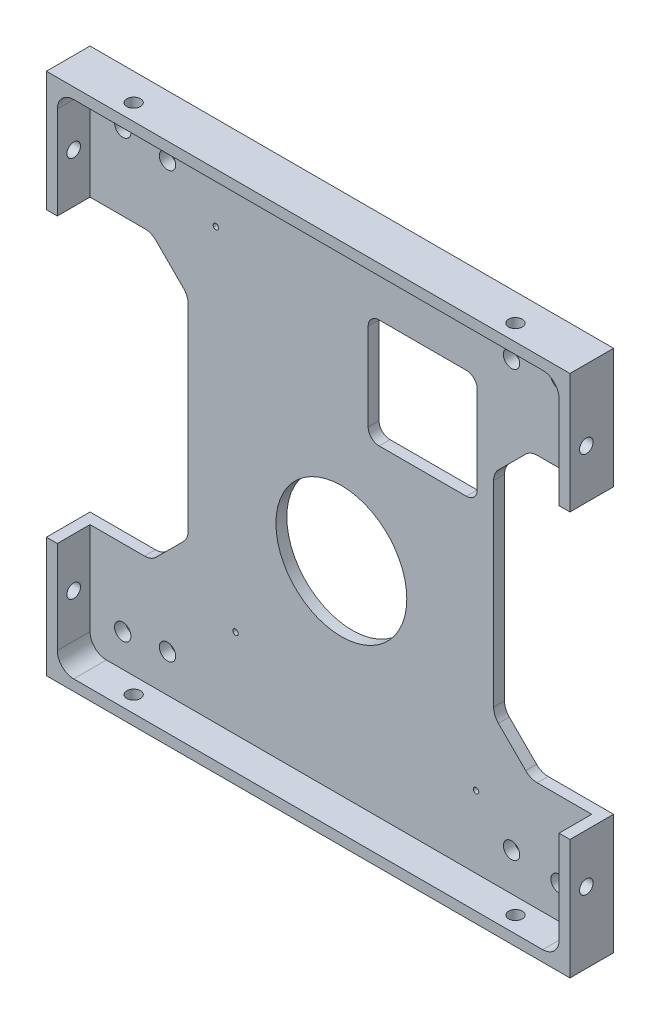
SolidWorks part; units mm, degrees
material "6061-T6 (SS)"
ref_plane "Front" through (0, 0, 0) normal (0, 0, 1) x (1, 0, 0)
ref_plane "Top" through (0, 0, 0) normal (0, 1, 0) x (1, 0, 0)
ref_plane "Right" through (0, 0, 0) normal (1, 0, 0) x (0, 0, -1)
sketch "Sketch1" plane through (0, 0, 0) normal (0, 0, 1) x (1, 0, 0)
  line L1 (-48, -48) -> (48, -48)
  line L2 (-48, -48) -> (-48, 48)
  line L3 (-48, 48) -> (48, 48)
  line L4 (48, -48) -> (48, 48)
  line L5 (-48, -48) -> (48, 48) construction
  line L6 (-48, 48) -> (48, -48) construction
  point P0 (0, 0)
  dimension "D1" = 96
  dimension "D2" = 96
extrude "Boss-Extrude1" add sketch "Sketch1" along normal blind 8
sketch "Sketch2" plane through (0, 0, 8) normal (0, 0, 1) x (1, 0, 0)
  line L1 (46, -46) -> (-46, -46)
  line L2 (46, -46) -> (46, 46)
  line L3 (46, 46) -> (-46, 46)
  line L4 (-46, -46) -> (-46, 46)
  line L5 (46, -46) -> (-46, 46) construction
  line L6 (46, 46) -> (-46, -46) construction
  point P0 (0, 0)
  dimension "D1" = 92
  dimension "D2" = 92
extrude "Component Platform" cut sketch "Sketch2" against normal blind 6
sketch "Sketch3" plane through (0, 0, 2) normal (0, 0, 1) x (1, 0, 0)
  line L1 (-33.8787, -25.1213) -> (-28.8787, -20.1213)
  line L2 (-33.8787, 25.1213) -> (-28.8787, 20.1213)
  line L3 (-28, -18) -> (-28, 18)
  line L4 (-48, -26) -> (-36, -26)
  line L7 (-48, 48) -> (-48, -48) construction
  line L8 (0, -56.7987) -> (0, 73.4321) construction
  line L9 (46, -46) -> (-57.8147, 57.8147) construction
  line L18 (46, 46) -> (-68.5705, -68.5705) construction
  line L23 (-48, 26) -> (-36, 26)
  line L26 (-48, -26) -> (-48, 26)
  line L28 (-48, -48) -> (48, -48) construction
  line L29 (48, -26) -> (48, 26)
  line L30 (48, 26) -> (36, 26)
  line L31 (33.8787, 25.1213) -> (28.8787, 20.1213)
  line L32 (28, -18) -> (28, 18)
  line L33 (33.8787, -25.1213) -> (28.8787, -20.1213)
  line L34 (48, -26) -> (36, -26)
  arc A3 (-28.8787, -20.1213) -> (-28, -18) centre (-31, -18) ccw
  arc A4 (-28.8787, 20.1213) -> (-28, 18) centre (-31, 18) cw
  arc A13 (-33.8787, -25.1213) -> (-36, -26) centre (-36, -23) cw
  arc A15 (-33.8787, 25.1213) -> (-36, 26) centre (-36, 23) ccw
  arc A17 (33.8787, 25.1213) -> (36, 26) centre (36, 23) cw
  arc A18 (28.8787, 20.1213) -> (28, 18) centre (31, 18) ccw
  arc A19 (28.8787, -20.1213) -> (28, -18) centre (31, -18) cw
  arc A20 (33.8787, -25.1213) -> (36, -26) centre (36, -23) ccw
  point P0 (-48, 0)
  point P37 (-48, 0)
  dimension "D2" = 3
  dimension "D3" = 3
  dimension "D4" = 20
  dimension "D6" = 3
  dimension "D7" = 3
  dimension "D8" = 135
  dimension "D5" = 52
  dimension "D9" = 135
  dimension "D10" = 12
  dimension "D11" = 12
  dimension "D12" = 48
extrude "Cable Slots" cut sketch "Sketch3" against normal mid plane 12
ref_plane "Center Y-Plane" through (0, 0, 0) normal (1, 0, 0) x (0, 0, -1)
ref_plane "Center X-Plane" through (0, 0, 0) normal (0, -1, 0) x (-1, 0, 0)
fillet "Inner Corner Fillets" radius 3 4 edges at (46, -46, 5) (-46, -46, 5) (46, 46, 5) (-46, 46, 5)
sketch "Sketch7" plane through (0, 0, 2) normal (0, 0, 1) x (1, 0, 0)
  line L0 (-48, -48) -> (48, -48) construction
  line L4 (48, -48) -> (48, -26) construction
  line L5 (48, 26) -> (48, 48) construction
  line L7 (48, 48) -> (-48, 48) construction
  line L8 (-43, -46) -> (43, -46) construction
  point P1 (-19.32, -29.75)
  point P4 (24.78, -32.85)
  point P5 (24.78, 32.85)
  point P8 (-22.92, 32.85)
  point P12 (24.7, -56.85)
  point P13 (24.7, 48)
  point P14 (-19.4, -48)
  point P15 (48, -32.85)
  point P16 (-48, -32.85)
  point P18 (-19.4, 48)
  point P19 (48, -32.85)
  point P20 (-48, -32.85)
  point P24 (48, 43.7)
  point P25 (-48.7506, 43.7)
  point P27 (48, 32.85)
  point P28 (-23, -48)
  point P29 (-23, 48)
  point P31 (-48.7506, 32.85)
  dimension "D1" = 16.25
  dimension "D2" = 47.7
  dimension "D3" = 15.15
  dimension "D4" = 23.22
  dimension "D5" = 23.22
  dimension "D6" = 44.1
  dimension "D7" = 15.15
  dimension "D8" = 15.15
sketch "Sketch9" plane through (0, 0, 2) normal (0, 0, 1) x (1, 0, 0)
  line L0 (25, 31) -> (25, 15)
  line L1 (23, 33) -> (7, 33)
  line L2 (23, 13) -> (7, 13)
  line L5 (5, 15) -> (5, 31)
  line L6 (48, 26) -> (48, 48) construction
  line L8 (48, 48) -> (-48, 48) construction
  arc A1 (25, 15) -> (23, 13) centre (23, 15) cw
  arc A2 (25, 31) -> (23, 33) centre (23, 31) ccw
  arc A3 (7, 33) -> (5, 31) centre (7, 31) ccw
  arc A4 (5, 15) -> (7, 13) centre (7, 15) ccw
  point P15 (25, 33)
  dimension "D1" = 2
  dimension "D6" = 2
  dimension "D7" = 16
  dimension "D2" = 20
  dimension "D3" = 16
  dimension "D4" = 15
  dimension "D5" = 23
sketch "Sketch11" plane through (48, 0, 0) normal (1, 0, 0) x (0, 0, -1)
  line L0 (-5, -48) -> (-5, 48) construction
  line L1 (-8, -48) -> (0, -48) construction
  line L2 (-8, 48) -> (0, 48) construction
  line L3 (-8, -48) -> (-8, -26) construction
  dimension "D1" = 3
sketch "Sketch12" plane through (0, 48, 0) normal (0, 1, 0) x (1, 0, 0)
  line L0 (-48, -5) -> (48, -5) construction
  line L1 (-48, -8) -> (-48, 0) construction
  line L2 (48, -8) -> (48, 0) construction
  line L3 (48, -8) -> (-48, -8) construction
  dimension "D1" = 3
hole_wizard "M3x0.5 Tapped Hole1" positions "Sketch13" profile "Sketch14" tap size "M3x0.5" standard "ANSI Metric"
sketch "Sketch13" plane through (48, 0, 0) normal (1, 0, 0) x (0, 0, -1)
  line L0 (-5, -48) -> (-5, 48) construction
  point P0 (-5, -35)
  point P4 (-5, 35)
  dimension "D1" = 70
  dimension "D2" = 35
sketch "Sketch14" plane through (48, -35, 5) normal (0, 1, 0) x (0, 0, -1)
  line L0 (0, 0) -> (0, 10.7511)
  line L1 (0, 10.7511) -> (1.25, 10)
  line L2 (1.25, 10) -> (1.25, 0)
  line L5 (1.25, 0) -> (0, 0)
  line L10 (0, 10.7511) -> (-1.25, 10) construction
  line L11 (0, -6.35) -> (0, 107.95) construction
  dimension "Tap Drill Dia." = 2.5
  dimension "Tap Drill Depth" = 10
  dimension "Drill Angle" = 118
hole_wizard "M3x0.5 Tapped Hole2" positions "Sketch15" profile "Sketch16" tap size "M3x0.5" standard "ANSI Metric"
sketch "Sketch15" plane through (0, 48, 0) normal (0, 1, 0) x (1, 0, 0)
  line L0 (-48, -5) -> (48, -5) construction
  point P0 (35, -5)
  point P4 (-35, -5)
  dimension "D1" = 70
  dimension "D2" = 35
sketch "Sketch16" plane through (35, 48, 5) normal (1, 0, 0) x (0, 0, 1)
  line L0 (0, 0) -> (0, 10.7511)
  line L1 (0, 10.7511) -> (1.25, 10)
  line L2 (1.25, 10) -> (1.25, 0)
  line L5 (1.25, 0) -> (0, 0)
  line L10 (0, 10.7511) -> (-1.25, 10) construction
  line L11 (0, -6.35) -> (0, 107.95) construction
  dimension "Tap Drill Dia." = 2.5
  dimension "Tap Drill Depth" = 10
  dimension "Drill Angle" = 118
mirror "Mirror1" about plane through (0, 0, 0) normal (1, 0, 0) of "M3x0.5 Tapped Hole1"
mirror "Mirror2" about plane through (0, 0, 0) normal (0, -1, 0) of "M3x0.5 Tapped Hole2"
sketch "Sketch22" plane through (0, 0, 2) normal (0, 0, 1) x (1, 0, 0)
  line L2 (46, -43) -> (46, -26) construction
  line L3 (-43, -46) -> (43, -46) construction
  line L4 (-46, -26) -> (-46, -43) construction
  line L6 (46, 26) -> (46, 43) construction
  line L7 (43, 46) -> (-43, 46) construction
  line L8 (-46, 43) -> (-46, 26) construction
  point P0 (-31.791, -39.06)
  point P1 (-31.791, 38.94)
  point P2 (31.29, 38.94)
  point P3 (31.29, -39.06)
  dimension "D1" = 14.71
  dimension "D2" = 6.94
  dimension "D3" = 6.94
  dimension "D4" = 14.209
  dimension "D5" = 14.71
  dimension "D6" = 7.06
  dimension "D7" = 7.06
  dimension "D8" = 14.209
hole_wizard "Ø1.0mm Dowel Hole1" positions "Sketch27" profile "Sketch28" hole size "Ø1.0" standard "ANSI Metric"
sketch "Sketch27" plane through (0, 0, 2) normal (0, 0, 1) x (1, 0, 0)
  point P0 (-19.32, -29.75)
  point P3 (24.78, -32.85)
  point P9 (-22.92, 32.85)
sketch "Sketch28" plane through (-19.32, -29.75, 2) normal (1, 0, 0) x (0, -1, 0)
  line L0 (0, 0) -> (0, 4.0004)
  line L1 (0, 4.0004) -> (0.5, 3.7)
  line L2 (0.5, 3.7) -> (0.5, 0)
  line L5 (0.5, 0) -> (0, 0)
  line L10 (0, 4.0004) -> (-0.5, 3.7) construction
  line L11 (0, -6.35) -> (0, 107.95) construction
  dimension "Hole Dia." = 1
  dimension "Hole Depth" = 3.7
  dimension "Drill Angle" = 118
sketch "Sketch29" plane through (0, 0, 0) normal (0, 0, -1) x (-1, 0, 0)
  line L0 (28, 18) -> (28, -18) construction
  line L2 (48, -48) -> (-48, -48) construction
  circle A0 centre (-0.0819, -8.7479) radius 12
  dimension "D1" = 24
  dimension "D2" = 28.0819
  dimension "D3" = 39.2521
extrude "HDD Extrusion Cutout" cut sketch "Sketch29" against normal blind 10
extrude "HDD Extrusion Cutout 2" cut sketch "Sketch9" against normal blind 10
hole_wizard "Ø3.0mm Dowel Hole1" positions "Sketch30" profile "Sketch31" hole size "Ø3.0" standard "ANSI Metric" end condition up to next
sketch "Sketch30" plane through (0, 0, 2) normal (0, 0, 1) x (1, 0, 0)
  point P0 (-31.791, -39.06)
  point P3 (31.29, -39.06)
  point P6 (31.29, 38.94)
  point P9 (-31.791, 38.94)
sketch "Sketch31" plane through (-31.791, -39.06, 2) normal (1, 0, 0) x (0, -1, 0)
  line L0 (0, 0) -> (0, 2)
  line L1 (0, 2) -> (1.5, 2)
  line L2 (1.5, 2) -> (1.5, 0)
  line L5 (1.5, 0) -> (0, 0)
  line L11 (0, -6.35) -> (0, 107.95) construction
  dimension "Thru Hole Dia." = 3
  dimension "Thru Hole Depth" = 2
sketch "Sketch32" plane through (0, 0, 2) normal (0, 0, 1) x (1, 0, 0)
  line L0 (0, -46) -> (0, 46) construction
  line L1 (-43, -46) -> (43, -46) construction
  line L2 (43, 46) -> (-43, 46) construction
  line L3 (48.3015, 0) -> (-47.2615, 0) construction
  line L5 (-48, -48) -> (48, -48) construction
  line L7 (40, 40) -> (-40, 40)
  line L8 (40, 40) -> (40, -40)
  line L9 (40, -40) -> (-40, -40)
  line L10 (-40, 40) -> (-40, -40)
  line L11 (40, 40) -> (-40, -40) construction
  line L12 (40, -40) -> (-40, 40) construction
  point P8 (0, 0)
  dimension "D1" = 48
  dimension "D2" = 80
  dimension "D3" = 80
hole_wizard "Ø3.0mm Dowel Hole2" positions "Sketch33" profile "Sketch34" hole size "Ø3.0" standard "ANSI Metric" end condition through all
sketch "Sketch33" plane through (0, 0, 2) normal (0, 0, 1) x (1, 0, 0)
  point P0 (40, -40)
  point P3 (-40, -40)
  point P6 (-40, 40)
  point P9 (40, 40)
sketch "Sketch34" plane through (40, -40, 2) normal (1, 0, 0) x (0, -1, 0)
  line L0 (0, 0) -> (0, 2)
  line L1 (0, 2) -> (1.5, 2)
  line L2 (1.5, 2) -> (1.5, 0)
  line L5 (1.5, 0) -> (0, 0)
  line L11 (0, -6.35) -> (0, 107.95) construction
  dimension "Thru Hole Dia." = 3
  dimension "Thru Hole Depth" = 2
